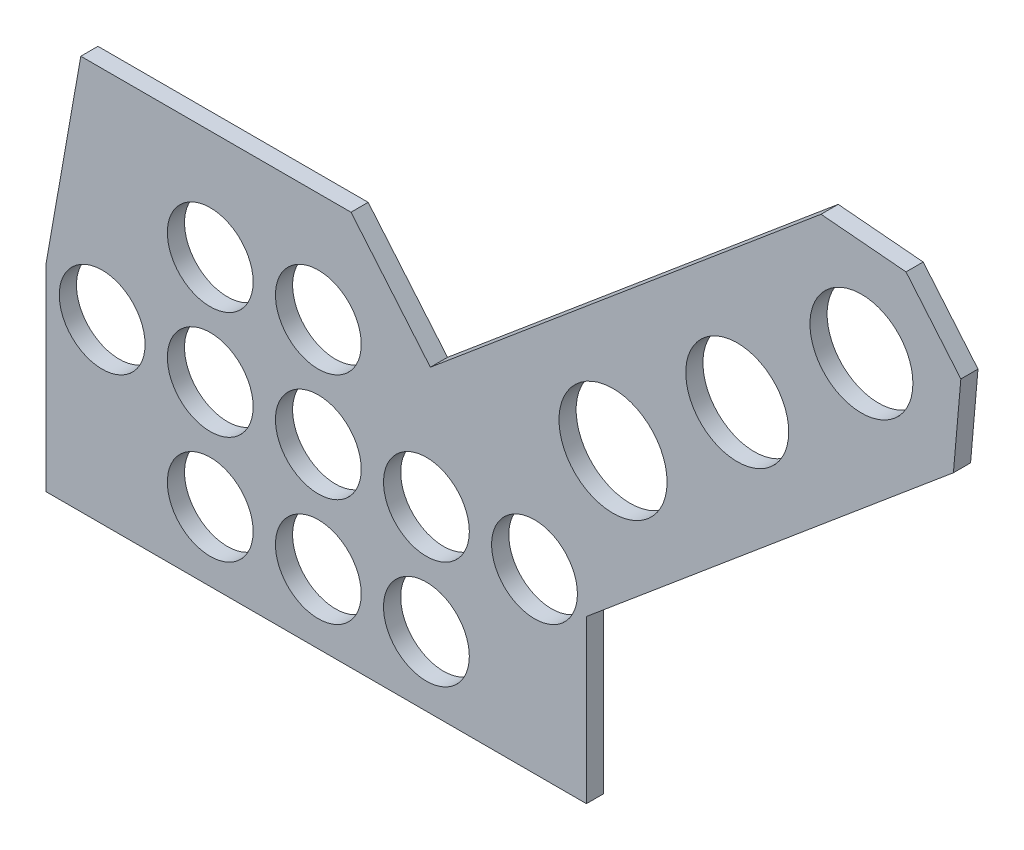
SolidWorks part; units mm, degrees
ref_plane "Front Plane" through (0, 0, 0) normal (0, 0, 1) x (1, 0, 0)
ref_plane "Top Plane" through (0, 0, 0) normal (0, 1, 0) x (1, 0, 0)
ref_plane "Right Plane" through (0, 0, 0) normal (1, 0, 0) x (0, 0, -1)
sketch "Sketch2" plane through (0, 0, 0) normal (0, 0, 1) x (1, 0, 0)
  line L23 (0, 0) -> (100, 0)
  line L24 (100, 0) -> (100, 30)
  line L25 (100, 30) -> (167.9013, 86.976)
  line L26 (167.9013, 86.976) -> (169.2768, 102.6974)
  line L27 (169.2768, 102.6974) -> (159.1326, 114.7868)
  line L28 (159.1326, 114.7868) -> (143.4111, 116.1622)
  line L31 (56.4359, 73) -> (6.4359, 73)
  line L32 (6.4359, 73) -> (0, 36.5)
  line L33 (0, 36.5) -> (0, 0)
  line L34 (164.2047, 108.7421) -> (100, 54.868) construction
  line L35 (56.4359, 73) -> (71.1187, 55.5017)
  line L36 (71.1187, 55.5017) -> (143.4111, 116.1622)
  line L37 (143.4111, 116.1622) -> (167.9013, 86.976) construction
  dimension "D1" = 130
  dimension "D2" = 50
  dimension "D3" = 73
  dimension "D4" = 30
  dimension "D5" = 101.6
  dimension "D6" = 100
  dimension "D7" = 38.1
  dimension "D8" = 170
  dimension "D9" = 36.5
extrude "Base Extrude" add sketch "Sketch2" along normal blind 3.175 contours L31 L32 L33 L23 L24 L25 L26 L27 L28 L36 L35
sketch "Sketch3" plane through (0, 0, 3.175) normal (0, 0, 1) x (1, 0, 0)
  line L0 (164.2047, 108.7421) -> (94.2774, 50.0662) construction
  line L1 (169.2768, 102.6974) -> (159.1326, 114.7868) construction
  circle A0 centre (150.8824, 97.5634) radius 9.525
  circle A1 centre (127.9011, 78.2798) radius 9.525
  circle A2 centre (104.9197, 58.9961) radius 10
  circle A3 centre (30.3915, 52.7667) radius 7.9375
  circle A4 centre (50.3915, 52.7667) radius 7.9375
  circle A5 centre (10.3915, 32.7667) radius 7.9375
  circle A6 centre (30.3915, 32.7667) radius 7.9375
  circle A7 centre (50.3915, 32.7667) radius 7.9375
  circle A8 centre (70.3915, 32.7667) radius 7.9375
  circle A9 centre (30.3915, 12.7667) radius 7.9375
  circle A10 centre (50.3915, 12.7667) radius 7.9375
  circle A11 centre (70.3915, 12.7667) radius 7.9375
  circle A12 centre (90.3915, 32.7667) radius 7.9375
  dimension "D1" = 15.875
  dimension "D2" = 20
  dimension "D11" = 19.05
  dimension "D3" = 30
  dimension "D4" = 20
  dimension "D5" = 20
  dimension "D6" = 20
  dimension "D7" = 20
  dimension "D8" = 20
  dimension "D9" = 20
  dimension "D10" = 30
extrude "Holes" cut sketch "Sketch3" against normal through all
